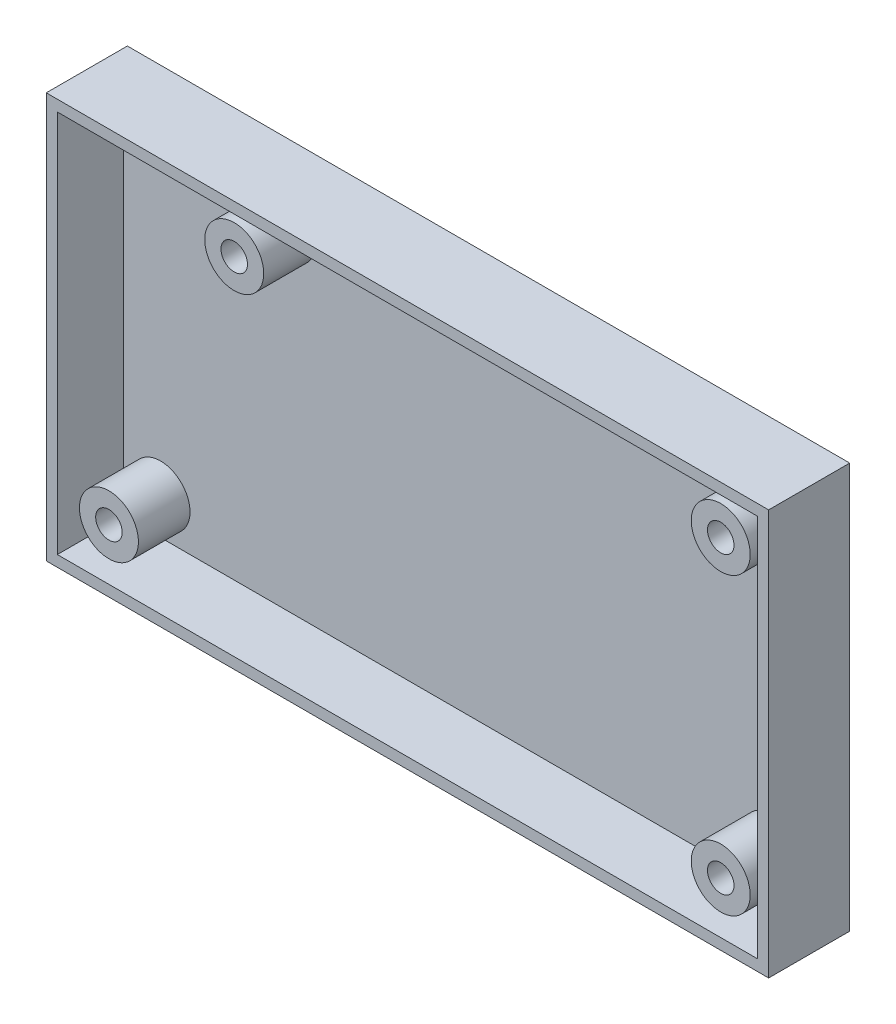
SolidWorks part; units mm, degrees
ref_plane "Front Plane" through (0, 0, 0) normal (0, 0, 1) x (1, 0, 0)
ref_plane "Top Plane" through (0, 0, 0) normal (0, 1, 0) x (1, 0, 0)
ref_plane "Right Plane" through (0, 0, 0) normal (1, 0, 0) x (0, 0, -1)
sketch "Sketch1" plane through (0, 0, 0) normal (0, 0, 1) x (1, 0, 0)
  line L1 (0, 0) -> (98, 0)
  line L2 (0, 0) -> (0, -55)
  line L3 (0, -55) -> (98, -55)
  line L4 (98, 0) -> (98, -55)
  dimension "D1" = 98
  dimension "D2" = 55
extrude "Boss-Extrude1" add sketch "Sketch1" along normal blind 2
sketch "Sketch2" plane through (0, 0, 2) normal (0, 0, 1) x (1, 0, 0)
  line L0 (98, -55) -> (98, 0) construction
  line L1 (0, -55) -> (98, -55) construction
  line L2 (0, 0) -> (0, -55) construction
  line L3 (98, 0) -> (0, 0) construction
  line L4 (98, -55) -> (98, 0)
  line L5 (0, -55) -> (98, -55)
  line L6 (0, 0) -> (0, -55)
  line L7 (98, 0) -> (0, 0)
  line L8 (96.5, -53.5) -> (96.5, -1.5)
  line L9 (96.5, -1.5) -> (1.5, -1.5)
  line L10 (1.5, -1.5) -> (1.5, -53.5)
  line L11 (1.5, -53.5) -> (96.5, -53.5)
  dimension "D1" = 1.5
extrude "Boss-Extrude2" add sketch "Sketch2" along normal blind 9
sketch "Sketch3" plane through (0, 0, 2) normal (0, 0, 1) x (1, 0, 0)
  line L0 (96.5, -53.5) -> (96.5, -1.5) construction
  line L1 (96.5, -1.5) -> (1.5, -1.5) construction
  line L3 (1.5, -53.5) -> (96.5, -53.5) construction
  line L4 (1.5, -1.5) -> (1.5, -53.5) construction
  line L5 (1.5, -1.5) -> (1.5, -53.5) construction
  circle A0 centre (89.5, -8.5) radius 1.8
  circle A1 centre (89.5, -48.5) radius 1.8
  circle A2 centre (6.5, -48.5) radius 1.8
  circle A3 centre (23.5, -8.5) radius 1.8
  circle A4 centre (89.5, -8.5) radius 4
  circle A5 centre (89.5, -48.5) radius 4
  circle A6 centre (6.5, -48.5) radius 4
  circle A7 centre (23.5, -8.5) radius 4
  dimension "D1" = 3.6
  dimension "D11" = 8
  dimension "D2" = 7
  dimension "D3" = 7
  dimension "D4" = 5
  dimension "D5" = 5
  dimension "D6" = 22
  dimension "D7" = 66
  dimension "D8" = 40
  dimension "D9" = 83
  dimension "D10" = 43.4626
extrude "Boss-Extrude3" add sketch "Sketch3" along normal blind 7
